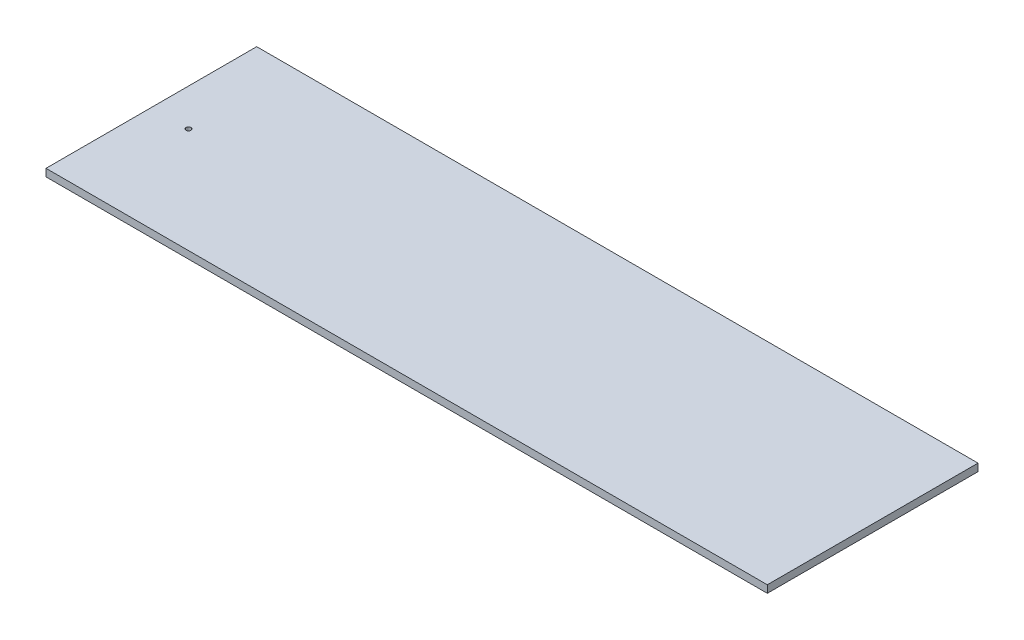
SolidWorks part; units mm, degrees
ref_plane "Front Plane" through (0, 0, 0) normal (0, 0, 1) x (1, 0, 0)
ref_plane "Top Plane" through (0, 0, 0) normal (0, 1, 0) x (1, 0, 0)
ref_plane "Right Plane" through (0, 0, 0) normal (1, 0, 0) x (0, 0, -1)
ref_plane "Plane1" through (0, 3, 0) normal (0, 1, 0) x (1, 0, 0)
sketch "Sketch1" plane through (0, 3, 0) normal (0, 1, 0) x (1, 0, 0)
  line L0 (-145.5, 42.5) -> (-145.5, -42.5)
  line L1 (-145.5, -42.5) -> (145.5, -42.5)
  line L2 (145.5, -42.5) -> (145.5, 42.5)
  line L3 (145.5, 42.5) -> (-145.5, 42.5)
  circle A0 centre (-130.5, 0) radius 1
extrude "Boss-Extrude1" add sketch "Sketch1" against normal blind 3
